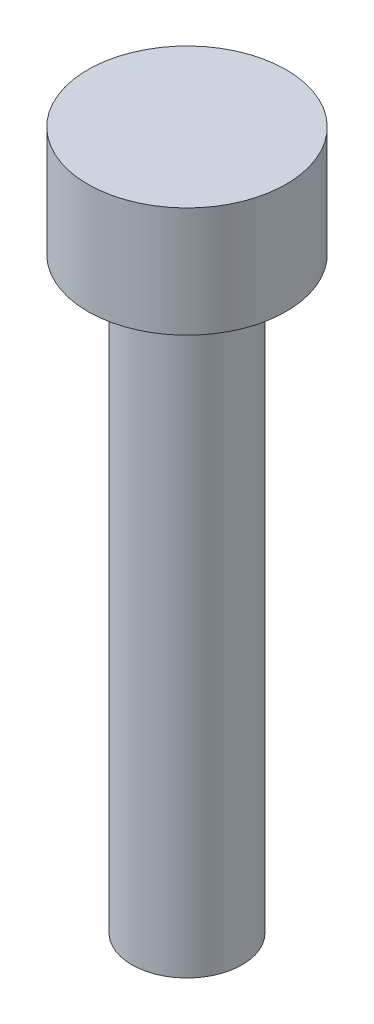
SolidWorks part; units mm, degrees
ref_plane "Front Plane" through (0, 0, 0) normal (0, 0, 1) x (1, 0, 0)
ref_plane "Top Plane" through (0, 0, 0) normal (0, 1, 0) x (1, 0, 0)
ref_plane "Right Plane" through (0, 0, 0) normal (1, 0, 0) x (0, 0, -1)
sketch "Sketch1" plane through (0, 0, 0) normal (0, 1, 0) x (1, 0, 0)
  circle A0 centre (0, 0) radius 1.5
  dimension "D1" = 3
extrude "Boss-Extrude1" add sketch "Sketch1" along normal blind 16
sketch "Sketch2" plane through (0, 16, 0) normal (0, 1, 0) x (1, 0, 0)
  circle A0 centre (0, 0) radius 2.7
  dimension "D1" = 5.4
extrude "Boss-Extrude2" add sketch "Sketch2" along normal blind 3
